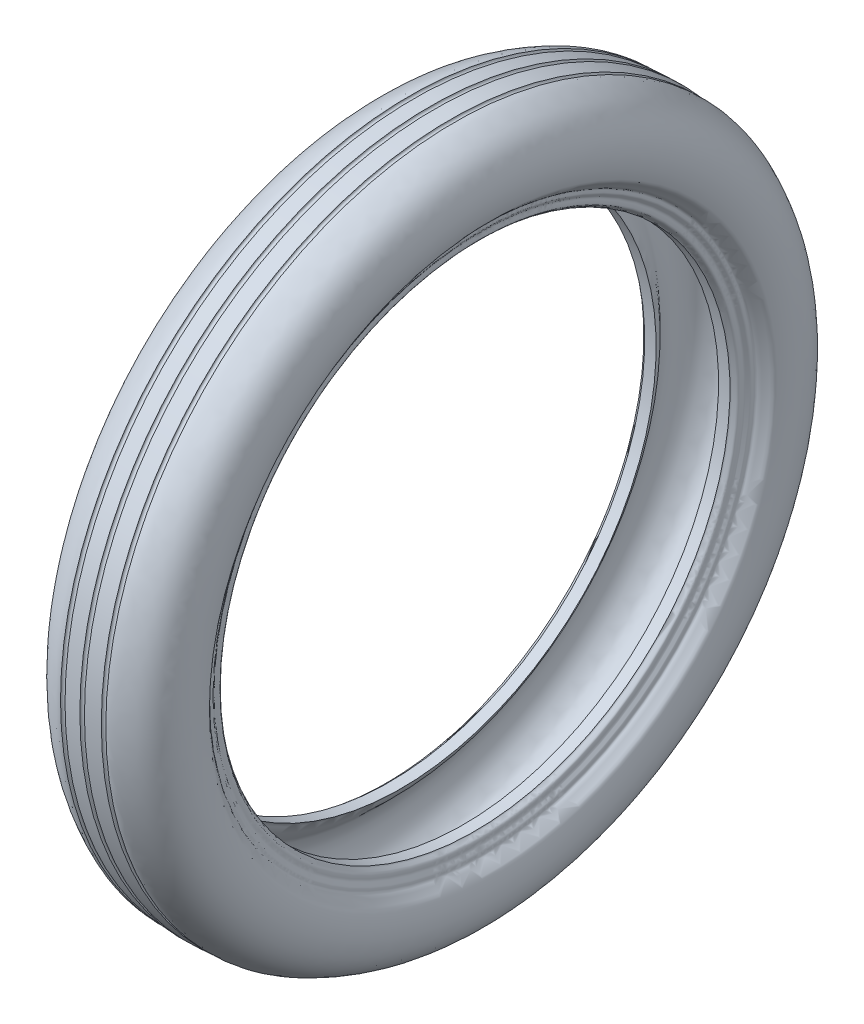
SolidWorks part; units mm, degrees
material "BUTYL"
ref_plane "Front Plane" through (0, 0, 0) normal (0, 0, 1) x (1, 0, 0)
ref_plane "Top Plane" through (0, 0, 0) normal (0, 1, 0) x (1, 0, 0)
ref_plane "Right Plane" through (0, 0, 0) normal (1, 0, 0) x (0, 0, -1)
sketch "Sketch1" plane through (0, 0, 0) normal (0, 0, 1) x (1, 0, 0)
  line L0 (51.6667, 341.5) -> (258.3333, 341.5) construction
  line L1 (43.3333, 103) -> (216.6667, 103) construction
  line L2 (0, 248.8346) -> (0, 0) construction
  line L3 (-24.8173, 203) -> (-33.9053, 203)
  line L4 (-14.4302, 277.4968) -> (-1.8191, 278.3033)
  line L5 (24.8173, 203) -> (33.9053, 203)
  line L6 (14.4302, 277.4968) -> (1.8191, 278.3033)
  line L7 (-102.7229, 0) -> (130.3407, 0) construction
  line L8 (-24.8173, 203) -> (24.8173, 203) construction
  arc A0 (-18.0013, 277.4968) -> (-14.4302, 277.4968) centre (-16.2157, 277.4968) ccw
  arc A1 (18.0013, 277.4968) -> (14.4302, 277.4968) centre (16.2157, 277.4968) cw
  arc A2 (-1.8191, 278.3033) -> (1.8191, 278.3033) centre (0, 278.3033) ccw
  spline S0 degree 3 poles (-24.8173, 203) (-27.2284, 205.0639) (-28.5496, 210.3276) (-33.6713, 215.0194) (-37.7773, 219.0104) (-42.2634, 223.062) (-45.1671, 229.5539) (-48.0287, 236.6578) (-47.888, 244.8825) (-46.3949, 254.0571) (-40.3487, 261.4036) (-33.8515, 268.8109) (-25.2444, 271.405) (-16.7423, 273.1864) (-10.1406, 273.4632) (-4.5443, 274.0141) (-1.7534, 273.4453) (0, 273.6518) knots 0 0 0 0 0.082233 0.137617 0.183009 0.237254 0.29747 0.371716 0.440605 0.515818 0.616104 0.690267 0.776014 0.84938 0.924773 0.95299 1 1 1 1
  spline S1 degree 3 poles (24.8173, 203) (27.2284, 205.0639) (28.5496, 210.3276) (33.6713, 215.0194) (37.7773, 219.0104) (42.2634, 223.062) (45.1671, 229.5539) (48.0287, 236.6578) (47.888, 244.8825) (46.3949, 254.0571) (40.3487, 261.4036) (33.8515, 268.8109) (25.2444, 271.405) (16.7423, 273.1864) (10.1406, 273.4632) (4.5443, 274.0141) (1.7534, 273.4453) (0, 273.6518) knots 0 0 0 0 0.082233 0.137617 0.183009 0.237254 0.29747 0.371716 0.440605 0.515818 0.616104 0.690267 0.776014 0.84938 0.924773 0.95299 1 1 1 1
  spline S2 degree 3 poles (-33.9053, 203) (-34.4514, 204.2233) (-38.4052, 205.2108) (-37.5895, 208.7025) (-37.3177, 211.6374) (-40.3679, 213.4652) (-39.0661, 217.0868) (-42.53, 218.9871) (-44.4812, 222.025) (-48.1613, 224.6642) (-49.3373, 231.2973) (-50.566, 239.2176) (-49.5419, 249.3098) (-46.4258, 258.7858) (-40.6849, 266.454) (-33.8688, 271.5447) (-26.5849, 275.2395) (-21.385, 277.7704) (-18.0013, 277.4968) knots 0 0 0 0 0.050285 0.080964 0.097206 0.139297 0.164562 0.195188 0.24242 0.280703 0.328072 0.440671 0.53315 0.638161 0.74644 0.823682 0.899585 1 1 1 1
  spline S3 degree 3 poles (33.9053, 203) (34.4514, 204.2233) (38.4052, 205.2108) (37.5895, 208.7025) (37.3177, 211.6374) (40.3679, 213.4652) (39.0661, 217.0868) (42.53, 218.9871) (44.4812, 222.025) (48.1613, 224.6642) (49.3373, 231.2973) (50.566, 239.2176) (49.5419, 249.3098) (46.4258, 258.7858) (40.6849, 266.454) (33.8688, 271.5447) (26.5849, 275.2395) (21.385, 277.7704) (18.0013, 277.4968) knots 0 0 0 0 0.050285 0.080964 0.097206 0.139297 0.164562 0.195188 0.24242 0.280703 0.328072 0.440671 0.53315 0.638161 0.74644 0.823682 0.899585 1 1 1 1
  dimension "D1" = 203
  dimension "D2" = 278.3033
revolve "Revolve2" add sketch "Sketch1" angle 360 about L7
sketch "Sketch3" plane through (0, 0, 0) normal (1, 0, 0) x (0, 0, -1)
  line L0 (0, 0) -> (0, -276.86)
  line L1 (0, -276.86) -> (50.8, -276.86)
  line L2 (50.8, -276.86) -> (40.8, -276.86)
  line L3 (50.8, -276.86) -> (50.8, -270.86)
  line L4 (40.8, -276.86) -> (40.8, -270.86)
  line L5 (50.8, -270.86) -> (40.8, -270.86)
  line L6 (50.8, -276.86) -> (60.8, -276.86)
  line L7 (50.8, -276.86) -> (50.8, -270.86)
  line L8 (60.8, -276.86) -> (60.8, -270.86)
  line L9 (50.8, -270.86) -> (60.8, -270.86)
  dimension "D1" = 276.86
  dimension "D2" = 50.8
  dimension "D3" = 6
  dimension "D4" = 10
  dimension "D5" = 10
move or copy body "Body-Move/Copy2" [suppressed] bodies to move or copy 102
move or copy body "Body-Move/Copy1" [suppressed] bodies to move or copy 102
